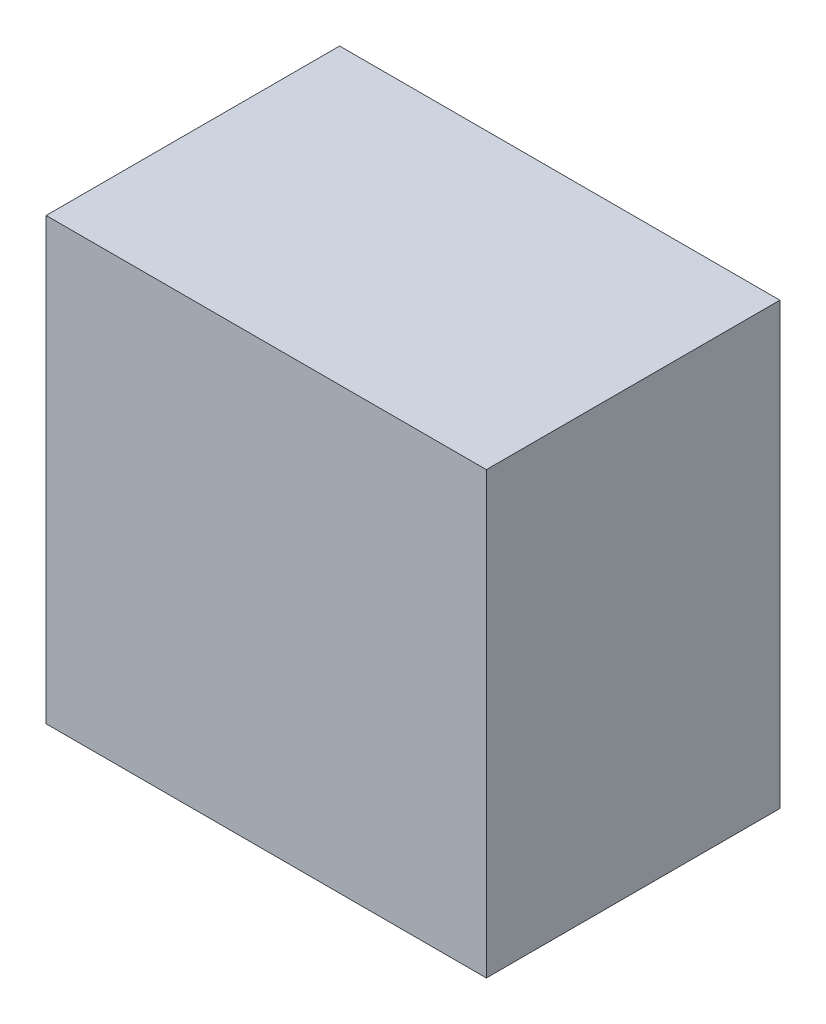
SolidWorks part; units mm, degrees
ref_plane "Front Plane" through (0, 0, 0) normal (0, 0, 1) x (1, 0, 0)
ref_plane "Top Plane" through (0, 0, 0) normal (0, 1, 0) x (1, 0, 0)
ref_plane "Right Plane" through (0, 0, 0) normal (1, 0, 0) x (0, 0, -1)
sketch "Sketch1" plane through (0, 0, 0) normal (0, 1, 0) x (1, 0, 0)
  line L1 (0, 0) -> (76.2, 0)
  line L2 (0, 0) -> (0, 50.8)
  line L3 (0, 50.8) -> (76.2, 50.8)
  line L4 (76.2, 0) -> (76.2, 50.8)
  dimension "D1" = 76.2
  dimension "D2" = 50.8
extrude "Boss-Extrude1" add sketch "Sketch1" along normal blind 76.2
